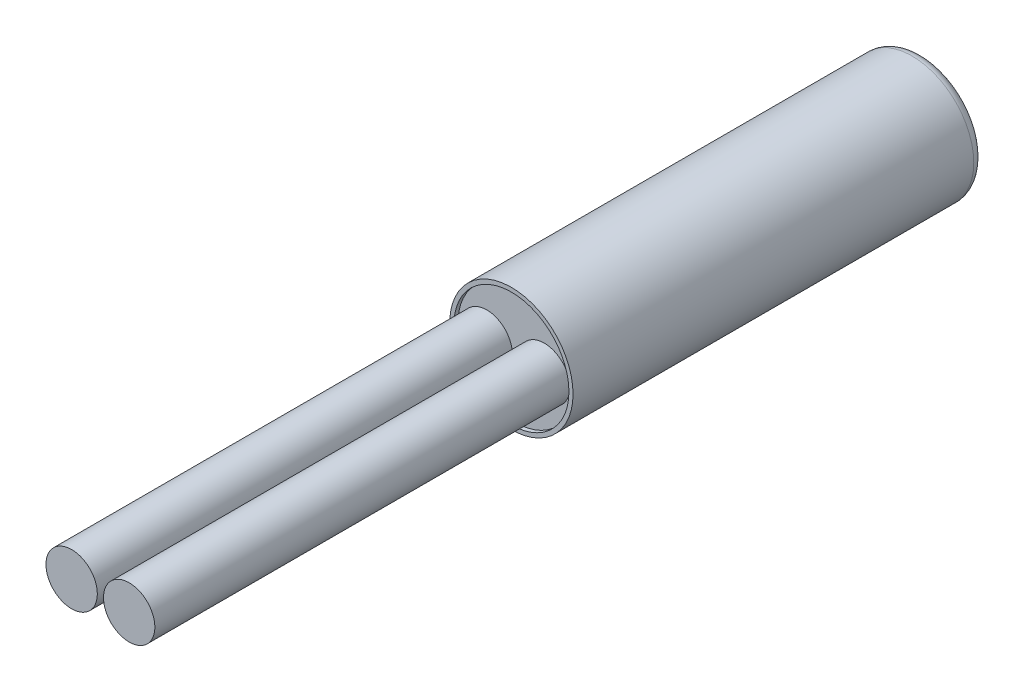
SolidWorks part; units mm, degrees
ref_plane "Plan de face" through (0, 0, 0) normal (0, 0, 1) x (1, 0, 0)
ref_plane "Plan de dessus" through (0, 0, 0) normal (0, 1, 0) x (1, 0, 0)
ref_plane "Plan de droite" through (0, 0, 0) normal (1, 0, 0) x (0, 0, -1)
sketch "Esquisse2" plane through (0, 0, 0) normal (0, 0, 1) x (1, 0, 0)
  circle A0 centre (0, 0) radius 3
extrude "Boss.-Extru.1" add sketch "Esquisse2" along normal blind 20
fillet "Congé1" radius 0.5 1 edges at (3, 0, 0)
sketch "Esquisse3" plane through (0, 0, 20) normal (0, 0, 1) x (1, 0, 0)
  circle A0 centre (0, 0) radius 2.8
extrude "Enlèv. mat.-Extru.1" cut sketch "Esquisse3" against normal blind 0.2
sketch "Esquisse4" plane through (0, 0, 19.8) normal (0, 0, 1) x (1, 0, 0)
  line L0 (0, 0) -> (2.8, 0) construction
  line L1 (2.8, 0) -> (1.4, 0) construction
  line L2 (1.4, 0) -> (0, 0) construction
  line L3 (0, 0) -> (-2.8, 0) construction
  line L4 (-2.8, 0) -> (-1.4, 0) construction
  circle A0 centre (0, 0) radius 2.8 construction
  circle A1 centre (-1.4, 0) radius 1.25
  circle A2 centre (1.4, 0) radius 1.25
extrude "Boss.-Extru.2" add sketch "Esquisse4" along normal blind 20.2
